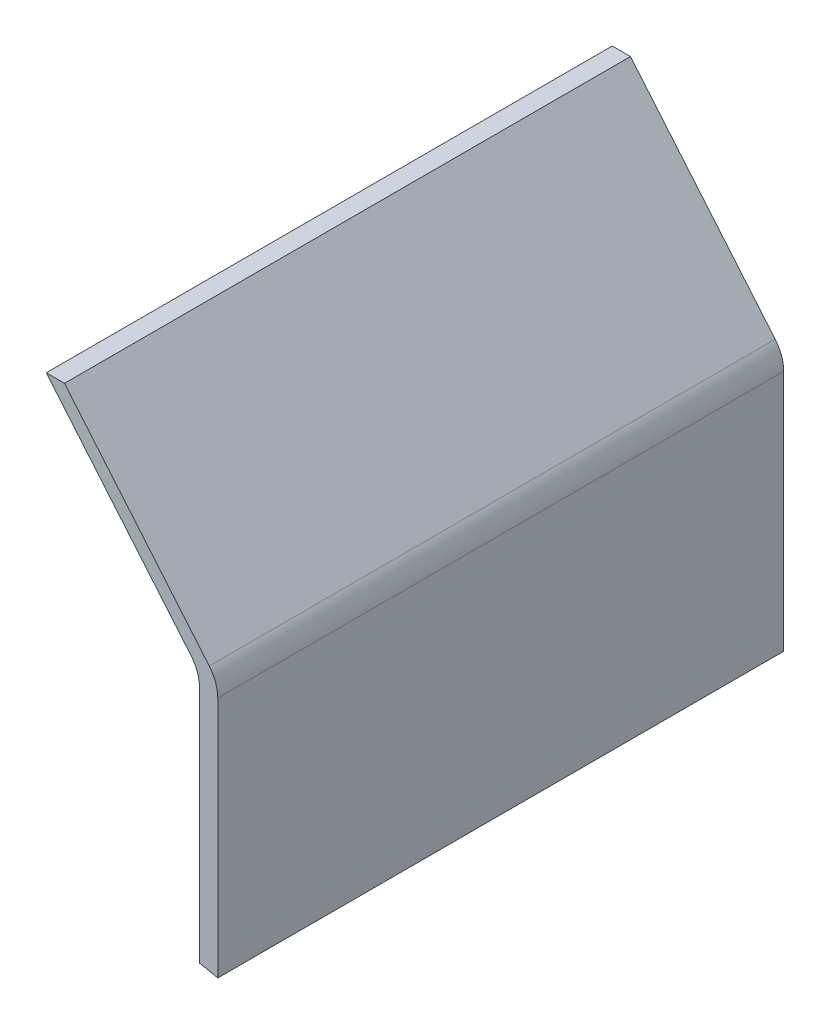
SolidWorks part; units mm, degrees
material "201 Annealed Stainless Steel (SS)"
ref_plane "Front Plane" through (0, 0, 0) normal (0, 0, 1) x (1, 0, 0)
ref_plane "Top Plane" through (0, 0, 0) normal (0, 1, 0) x (1, 0, 0)
ref_plane "Right Plane" through (0, 0, 0) normal (1, 0, 0) x (0, 0, -1)
sketch "Sketch1" plane through (0, 0, 0) normal (0, 0, 1) x (1, 0, 0)
  line L1 (-5, 1.0374) -> (-5, 70.0374)
  line L2 (-5, 70.0374) -> (-46.974, 120.0601)
  line L3 (-46.974, 120.0601) -> (-41.974, 120.0601)
  line L4 (-41.974, 120.0601) -> (0, 70.0374)
  line L5 (0, 70.0374) -> (0, 0)
  line L6 (-35, -156.1249) -> (-35, 3.8751) construction
  line L7 (-35, -156.1249) -> (0, -156.1249) construction
  line L8 (0, -156.1249) -> (0, 0) construction
  arc A0 (0, 0) -> (-5, 1.0374) centre (-35, -156.1249) ccw
  dimension "D6" = 320
  dimension "D3" = 5
  dimension "D1" = 69
  dimension "D2" = 5
  dimension "D4" = 140
  dimension "D5" = 65.3
  dimension "D7" = 35
extrude "Funnel - Left Side" add sketch "Sketch1" along normal blind 155
fillet "Fillet1" radius 10 2 edges at (0, 70.0374, 77.5) (-5, 70.0374, 77.5)
